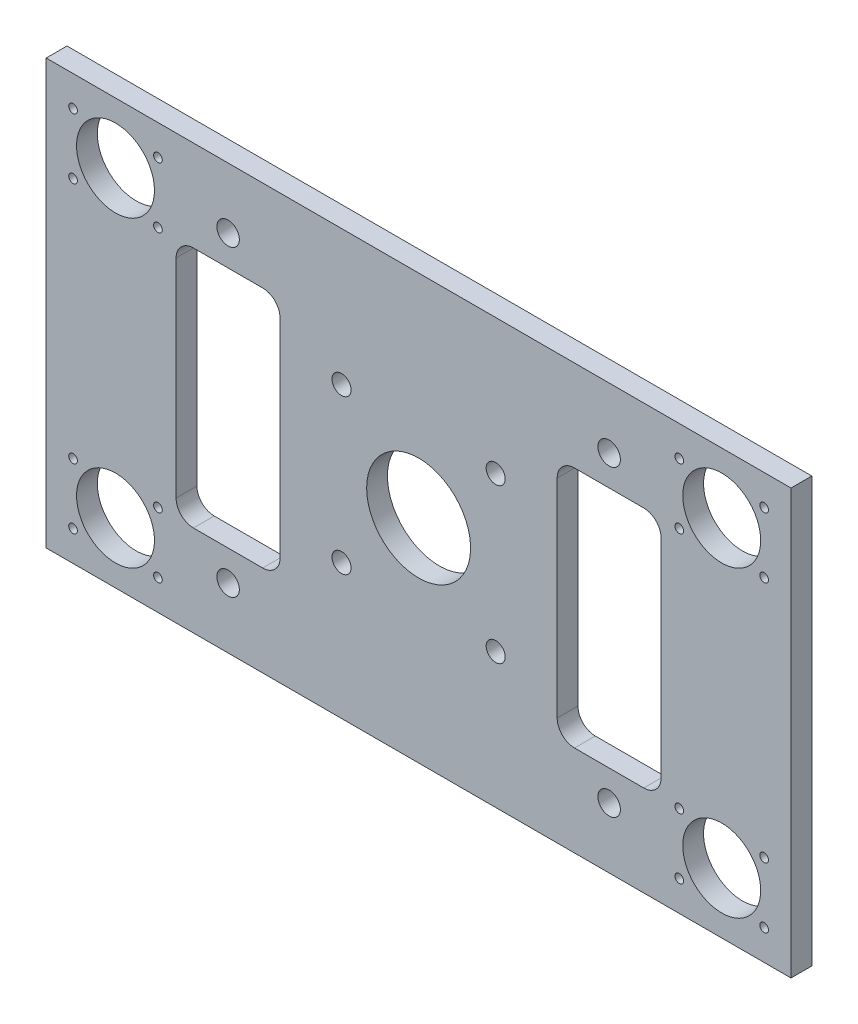
SolidWorks part; units mm, degrees
material "A3钢"
ref_plane "前视基准面" through (0, 0, 0) normal (0, 0, 1) x (1, 0, 0)
ref_plane "上视基准面" through (0, 0, 0) normal (0, 1, 0) x (1, 0, 0)
ref_plane "右视基准面" through (0, 0, 0) normal (1, 0, 0) x (0, 0, -1)
sketch "草图1" plane through (0, 0, 0) normal (0, 0, 1) x (1, 0, 0)
  line L1 (-215, -122.5) -> (215, -122.5)
  line L2 (-215, -122.5) -> (-215, 122.5)
  line L3 (-215, 122.5) -> (215, 122.5)
  line L4 (215, -122.5) -> (215, 122.5)
  line L5 (-215, -122.5) -> (215, 122.5) construction
  line L6 (-215, 122.5) -> (215, -122.5) construction
  point P0 (0, 0)
  dimension "D1" = 430
  dimension "D2" = 245
extrude "凸台-拉伸1" add sketch "草图1" along normal mid plane 12
sketch "草图2" plane through (0, 0, 6) normal (0, 0, 1) x (1, 0, 0)
  line L0 (-235.4398, 0) -> (243.2081, 0) construction
  line L1 (0, 138.3358) -> (0, -134.7504) construction
  circle A0 centre (-175, 87.5) radius 22.5
  circle A1 centre (175, 87.5) radius 22.5
  circle A2 centre (175, -87.5) radius 22.5
  circle A3 centre (-175, -87.5) radius 22.5
  dimension "D1" = 350
  dimension "D2" = 175
  dimension "D3" = 45
extrude "切除-拉伸1" cut sketch "草图2" against normal through all
hole_wizard "M6 螺纹孔1" positions "草图3" profile "草图4" tap size "M6" standard "GB" end condition through all
sketch "草图3" plane through (0, 0, 6) normal (0, 0, 1) x (1, 0, 0)
  line L0 (-175, 87.5) -> (-240.9373, 87.5) construction
  line L3 (-175, 87.5) -> (-175, 143.0566) construction
  line L7 (-248.1081, 0) -> (258.1472, 0) construction
  line L10 (0, 162.4176) -> (0, -160.2664) construction
  point P0 (-199.5, 105)
  point P16 (-150.5, 105)
  point P17 (-150.5, 70)
  point P18 (-199.5, 70)
  point P32 (199.5, 70)
  point P33 (150.5, 70)
  point P34 (150.5, 105)
  point P35 (199.5, 105)
  point P36 (199.5, -105)
  point P37 (150.5, -105)
  point P38 (150.5, -70)
  point P39 (199.5, -70)
  point P40 (-199.5, -70)
  point P41 (-150.5, -70)
  point P42 (-150.5, -105)
  point P43 (-199.5, -105)
  dimension "D1" = 49
  dimension "D2" = 35
sketch "草图4" plane through (-199.5, 105, 6) normal (1, 0, 0) x (0, -1, 0)
  line L0 (0, 0) -> (0, 12)
  line L1 (0, 12) -> (2.5, 12)
  line L2 (2.5, 12) -> (2.5, 0)
  line L5 (2.5, 0) -> (0, 0)
  line L11 (0, -6.35) -> (0, 107.95) construction
  dimension "通孔螺纹孔钻头直径" = 5
  dimension "通孔螺纹孔钻头深度" = 12
cosmetic thread "孔螺蚊线1" parameters "D2"=6
cosmetic thread "孔螺蚊线2" parameters "D2"=6
cosmetic thread "孔螺蚊线3" parameters "D2"=6
cosmetic thread "孔螺蚊线4" parameters "D2"=6
cosmetic thread "孔螺蚊线5" parameters "D2"=6
cosmetic thread "孔螺蚊线6" parameters "D2"=6
cosmetic thread "孔螺蚊线7" parameters "D2"=6
cosmetic thread "孔螺蚊线8" parameters "D2"=6
cosmetic thread "孔螺蚊线9" parameters "D2"=6
cosmetic thread "孔螺蚊线10" parameters "D2"=6
cosmetic thread "孔螺蚊线11" parameters "D2"=6
cosmetic thread "孔螺蚊线12" parameters "D2"=6
cosmetic thread "孔螺蚊线13" parameters "D2"=6
cosmetic thread "孔螺蚊线14" parameters "D2"=6
cosmetic thread "孔螺蚊线15" parameters "D2"=6
cosmetic thread "孔螺蚊线16" parameters "D2"=6
sketch "草图5" plane through (0, 0, 6) normal (0, 0, 1) x (1, 0, 0)
  line L1 (-130, -70) -> (130, -70)
  line L2 (-140, -60) -> (-140, 60)
  line L3 (-130, 70) -> (130, 70)
  line L4 (140, -60) -> (140, 60)
  line L5 (-140, -70) -> (140, 70) construction
  line L6 (-140, 70) -> (140, -70) construction
  arc A0 (-130, -70) -> (-140, -60) centre (-130, -60) cw
  arc A1 (130, -70) -> (140, -60) centre (130, -60) ccw
  arc A2 (130, 70) -> (140, 60) centre (130, 60) cw
  arc A3 (-140, 60) -> (-130, 70) centre (-130, 60) cw
  point P0 (0, 0)
  dimension "D3" = 10
  dimension "D1" = 280
  dimension "D2" = 140
extrude "切除-拉伸2" cut sketch "草图5" against normal through all
hole_wizard "Ø13.0 (13) 直径孔1" positions "草图6" profile "草图7" hole size "Ø13.0" standard "GB" end condition through all
sketch "草图6" plane through (0, 0, -6) normal (0, 0, -1) x (-1, 0, 0)
  line L0 (-240.2045, 0) -> (240.2045, 0) construction
  line L3 (0, 136.6997) -> (0, -144.3396) construction
  point P0 (-110, 87.5)
  point P14 (110, 87.5)
  point P15 (110, -87.5)
  point P16 (-110, -87.5)
  dimension "D1" = 220
  dimension "D2" = 175
sketch "草图7" plane through (110, 87.5, -6) normal (1, 0, 0) x (0, 1, 0)
  line L0 (0, 0) -> (0, 12)
  line L1 (0, 12) -> (6.5, 12)
  line L2 (6.5, 12) -> (6.5, 0)
  line L5 (6.5, 0) -> (0, 0)
  line L11 (0, -6.35) -> (0, 107.95) construction
  dimension "通孔孔直径" = 13
  dimension "通孔孔深度" = 12
sketch "草图8" plane through (0, 0, -6) normal (0, 0, -1) x (-1, 0, 0)
  line L0 (-130, 70) -> (130, 70) construction
  line L1 (-80, 70) -> (80, 70)
  line L2 (-80, 70) -> (-80, 95)
  line L3 (-70, 105) -> (70, 105)
  line L4 (80, 70) -> (80, 95)
  line L5 (0, 142.1043) -> (0, -140.7366) construction
  line L6 (239.604, 0) -> (-237.8025, 0) construction
  line L7 (80, -70) -> (80, -95)
  line L8 (-70, -105) -> (70, -105)
  line L9 (-80, -70) -> (-80, -95)
  line L10 (-80, -70) -> (80, -70)
  arc A0 (70, 105) -> (80, 95) centre (70, 95) cw
  arc A1 (-80, 95) -> (-70, 105) centre (-70, 95) cw
  arc A2 (-80, -95) -> (-70, -105) centre (-70, -95) ccw
  arc A3 (70, -105) -> (80, -95) centre (70, -95) ccw
  point P14 (80, 105)
  point P17 (-80, 105)
  dimension "D1" = 10
  dimension "D2" = 35
  dimension "D3" = 160
extrude "切除-拉伸3" cut sketch "草图8" against normal through all
sketch "草图9" plane through (0, 0, -6) normal (0, 0, -1) x (-1, 0, 0)
  line L0 (70, 105) -> (-70, 105) construction
  line L1 (-70, -105) -> (70, -105)
  line L2 (-80, -95) -> (-80, 95)
  line L3 (-70, 105) -> (70, 105)
  line L4 (80, -95) -> (80, 95)
  line L5 (-80, -105) -> (80, 105) construction
  line L6 (-80, 105) -> (80, -105) construction
  line L7 (80, 70) -> (80, 95) construction
  arc A0 (-70, -105) -> (-80, -95) centre (-70, -95) cw
  arc A1 (70, -105) -> (80, -95) centre (70, -95) ccw
  arc A2 (-80, 95) -> (-70, 105) centre (-70, 95) cw
  arc A3 (70, 105) -> (80, 95) centre (70, 95) cw
  point P0 (0, 0)
  dimension "D1" = 10
sketch "草图10" plane through (0, 0, -6) normal (0, 0, -1) x (-1, 0, 0)
  line L0 (-80, -70) -> (-80, -95) construction
  line L1 (-70, -105) -> (70, -105) construction
  line L2 (80, -95) -> (80, -70) construction
  line L3 (80, 70) -> (80, 95) construction
  line L4 (70, 105) -> (-70, 105) construction
  line L5 (-80, 95) -> (-80, 70) construction
  line L6 (-80, -70) -> (-80, -95)
  line L7 (-70, -105) -> (70, -105)
  line L8 (80, -95) -> (80, -70)
  line L9 (80, 70) -> (80, 95)
  line L10 (70, 105) -> (-70, 105)
  line L11 (-80, 95) -> (-80, 70)
  line L12 (-80, 70) -> (-80, -70)
  line L13 (80, 70) -> (80, -70)
  arc A0 (-80, -95) -> (-70, -105) centre (-70, -95) ccw construction
  arc A1 (70, -105) -> (80, -95) centre (70, -95) ccw construction
  arc A2 (80, 95) -> (70, 105) centre (70, 95) ccw construction
  arc A3 (-70, 105) -> (-80, 95) centre (-70, 95) ccw construction
  arc A4 (-80, -95) -> (-70, -105) centre (-70, -95) ccw
  arc A5 (70, -105) -> (80, -95) centre (70, -95) ccw
  arc A6 (80, 95) -> (70, 105) centre (70, 95) ccw
  arc A7 (-70, 105) -> (-80, 95) centre (-70, 95) ccw
extrude "凸台-拉伸2" add sketch "草图10" against normal up to surface (12 mm away) up to face at (0, 0, 6)
fillet "圆角1" radius 10 4 edges at (80, -70, 0) (80, 70, 0) (-80, -70, 0) (-80, 70, 0)
sketch "草图11" plane through (0, 0, -6) normal (0, 0, -1) x (-1, 0, 0)
  circle A0 centre (0, 0) radius 30
  dimension "D1" = 60
extrude "切除-拉伸4" cut sketch "草图11" against normal through all
sketch "草图12" plane through (0, 0, -6) normal (0, 0, -1) x (-1, 0, 0)
  line L1 (-44.5, -44.5) -> (44.5, -44.5)
  line L2 (-44.5, -44.5) -> (-44.5, 44.5)
  line L3 (-44.5, 44.5) -> (44.5, 44.5)
  line L4 (44.5, -44.5) -> (44.5, 44.5)
  line L5 (-44.5, -44.5) -> (44.5, 44.5) construction
  line L6 (-44.5, 44.5) -> (44.5, -44.5) construction
  point P0 (0, 0)
  dimension "D1" = 89
hole_wizard "Ø11.0 (11) 直径孔1" positions "3D草图1" profile "草图13" hole size "Ø11.0" standard "GB" end condition through all
sketch3d "3D草图1"
  point P0 (44.5, 44.5, -6)
  point P3 (-44.5, 44.5, -6)
  point P6 (-44.5, -44.5, -6)
  point P9 (44.5, -44.5, -6)
sketch "草图13" plane through (44.5, 44.5, -6) normal (1, 0, 0) x (0, 1, 0)
  line L0 (0, 0) -> (0, 12)
  line L1 (0, 12) -> (5.5, 12)
  line L2 (5.5, 12) -> (5.5, 0)
  line L5 (5.5, 0) -> (0, 0)
  line L11 (0, -6.35) -> (0, 107.95) construction
  dimension "通孔孔直径" = 11
  dimension "通孔孔深度" = 12
